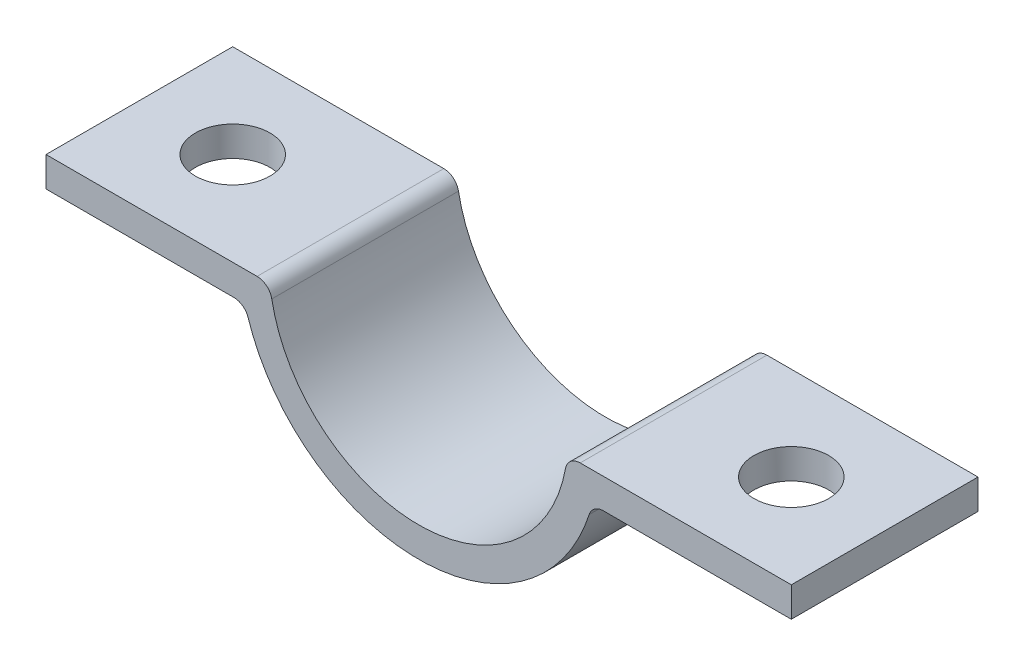
SolidWorks part; units mm, degrees
ref_plane "Front Plane" through (0, 0, 0) normal (0, 0, 1) x (1, 0, 0)
ref_plane "Top Plane" through (0, 0, 0) normal (0, 1, 0) x (1, 0, 0)
ref_plane "Right Plane" through (0, 0, 0) normal (1, 0, 0) x (0, 0, -1)
sketch "Sketch3" plane through (0, 0, 0) normal (0, 0, 1) x (1, 0, 0)
  line L0 (0, 0) -> (0, 50000) construction
  line L1 (0, 0) -> (50000, 0) construction
  line L2 (0, 0) -> (0, 20.0173) construction
  line L15 (0, 20.0173) -> (0, 19.0173) construction
  line L16 (-10.8167, 19.0173) -> (-19.9499, 19.0173)
  line L18 (-19.9499, 17.0173) -> (-12.3693, 17.0173)
  line L19 (10.8167, 19.0173) -> (19.9499, 19.0173)
  line L21 (19.9499, 17.0173) -> (12.3693, 17.0173)
  line L22 (-19.9499, 19.0173) -> (-24.9499, 19.0173)
  line L23 (-24.9499, 19.0173) -> (-24.9499, 17.0173)
  line L24 (-24.9499, 17.0173) -> (-19.9499, 17.0173)
  line L25 (19.9499, 19.0173) -> (24.9499, 19.0173)
  line L26 (24.9499, 19.0173) -> (24.9499, 17.0173)
  line L27 (24.9499, 17.0173) -> (19.9499, 17.0173)
  arc A0 (-9.8333, 18.1991) -> (9.8333, 18.1991) centre (0, 20.0173) ccw
  arc A3 (-11.4178, 16.325) -> (11.4178, 16.325) centre (0, 20.0173) ccw
  arc A4 (10.8167, 19.0173) -> (9.8333, 18.1991) centre (10.8167, 18.0173) ccw
  arc A5 (12.3693, 17.0173) -> (11.4178, 16.325) centre (12.3693, 16.0173) ccw
  arc A6 (-10.8167, 19.0173) -> (-9.8333, 18.1991) centre (-10.8167, 18.0173) cw
  arc A7 (-12.3693, 17.0173) -> (-11.4178, 16.325) centre (-12.3693, 16.0173) cw
  point P18 (9.9499, 19.0173)
  point P21 (11.619, 17.0173)
  point P24 (-9.9499, 19.0173)
  point P27 (-11.619, 17.0173)
  dimension "D1" = 1
extrude "Boss-Extrude2" add sketch "Sketch3" along normal blind 12.5
sketch "Sketch4" plane through (0, 19.0173, 0) normal (0, 1, 0) x (1, 0, 0)
  line L0 (-24.9499, -6.25) -> (-18.6999, -6.25) construction
  line L2 (0, 0) -> (0, -12.5) construction
  line L3 (-9.8333, -12.5) -> (9.8333, -12.5) construction
  line L4 (-24.9499, -12.5) -> (-24.9499, 0) construction
  circle A2 centre (-18.6999, -6.25) radius 2.5
  circle A3 centre (18.6999, -6.25) radius 2.5
extrude "Cut-Extrude1" cut sketch "Sketch4" against normal up to next
